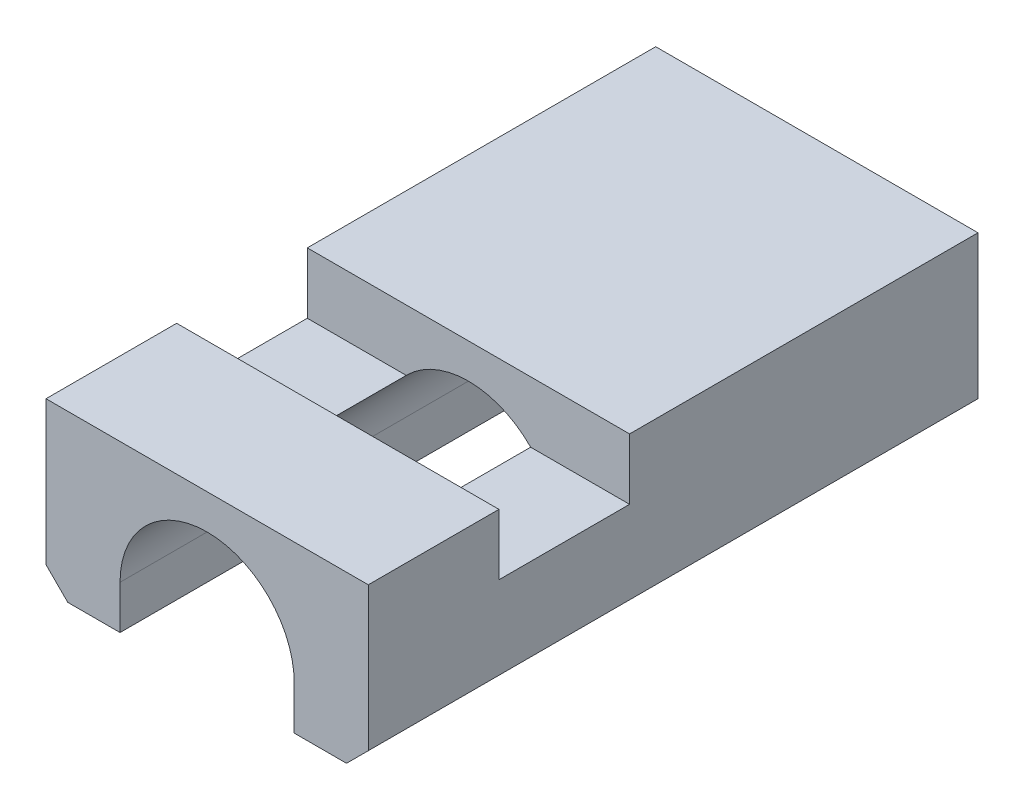
SolidWorks part; units mm, degrees
ref_plane "Front Plane" through (0, 0, 0) normal (0, 0, 1) x (1, 0, 0)
ref_plane "Top Plane" through (0, 0, 0) normal (0, 1, 0) x (1, 0, 0)
ref_plane "Right Plane" through (0, 0, 0) normal (1, 0, 0) x (0, 0, -1)
sketch "Sketch1" plane through (0, 0, 0) normal (0, 0, 1) x (1, 0, 0)
  line L0 (-23.1713, 58.5489) -> (-23.1713, 56.5489) construction
  line L1 (-26.8713, 53.7489) -> (-26.8713, 52.7489)
  line L2 (-26.8713, 53.7489) -> (-19.4713, 53.7489) construction
  line L3 (-26.8713, 53.7489) -> (-26.8713, 56.5489)
  line L4 (-26.8713, 56.5489) -> (-19.4713, 56.5489)
  line L5 (-19.4713, 53.7489) -> (-19.4713, 56.5489)
  line L6 (-26.8713, 52.7489) -> (-25.1713, 52.7489)
  line L7 (-25.1713, 52.7489) -> (-25.1713, 53.7489)
  line L8 (-21.1713, 53.7489) -> (-21.1713, 52.7489)
  line L9 (-21.1713, 52.7489) -> (-19.4713, 52.7489)
  line L10 (-19.4713, 52.7489) -> (-19.4713, 53.7489)
  line L11 (-23.1713, 56.5489) -> (-23.1713, 53.7489) construction
  circle A1 centre (-23.1713, 53.7489) radius 3.7 construction
  circle A2 centre (-23.1713, 53.7489) radius 2 construction
  arc A3 (-25.1713, 53.7489) -> (-21.1713, 53.7489) centre (-23.1713, 53.7489) cw
  dimension "D1" = 7.4
  dimension "D2" = 4
  dimension "D3" = 2
  dimension "D4" = 2.8
  dimension "D5" = 1
extrude "Boss-Extrude1" add sketch "Sketch1" along normal blind 14
chamfer "Chamfer1" distance 0.5 angle 45 2 edges at (-19.4713, 52.7489, 7) (-26.8713, 52.7489, 7)
sketch "Sketch2" plane through (-19.4713, 0, 0) normal (1, 0, 0) x (0, 0, -1)
  line L0 (-14, 56.5489) -> (0, 56.5489) construction
  line L1 (-11, 56.5489) -> (-8, 56.5489)
  line L2 (-11, 56.5489) -> (-11, 55.1489)
  line L3 (-11, 55.1489) -> (-8, 55.1489)
  line L4 (-8, 56.5489) -> (-8, 55.1489)
  line L5 (-11, 55.8489) -> (-14, 55.8489) construction
  line L6 (-14, 53.2489) -> (-14, 56.5489) construction
  dimension "D1" = 1.4
  dimension "D2" = 3
  dimension "D3" = 3
extrude "Cut-Extrude1" cut sketch "Sketch2" against normal blind 15
